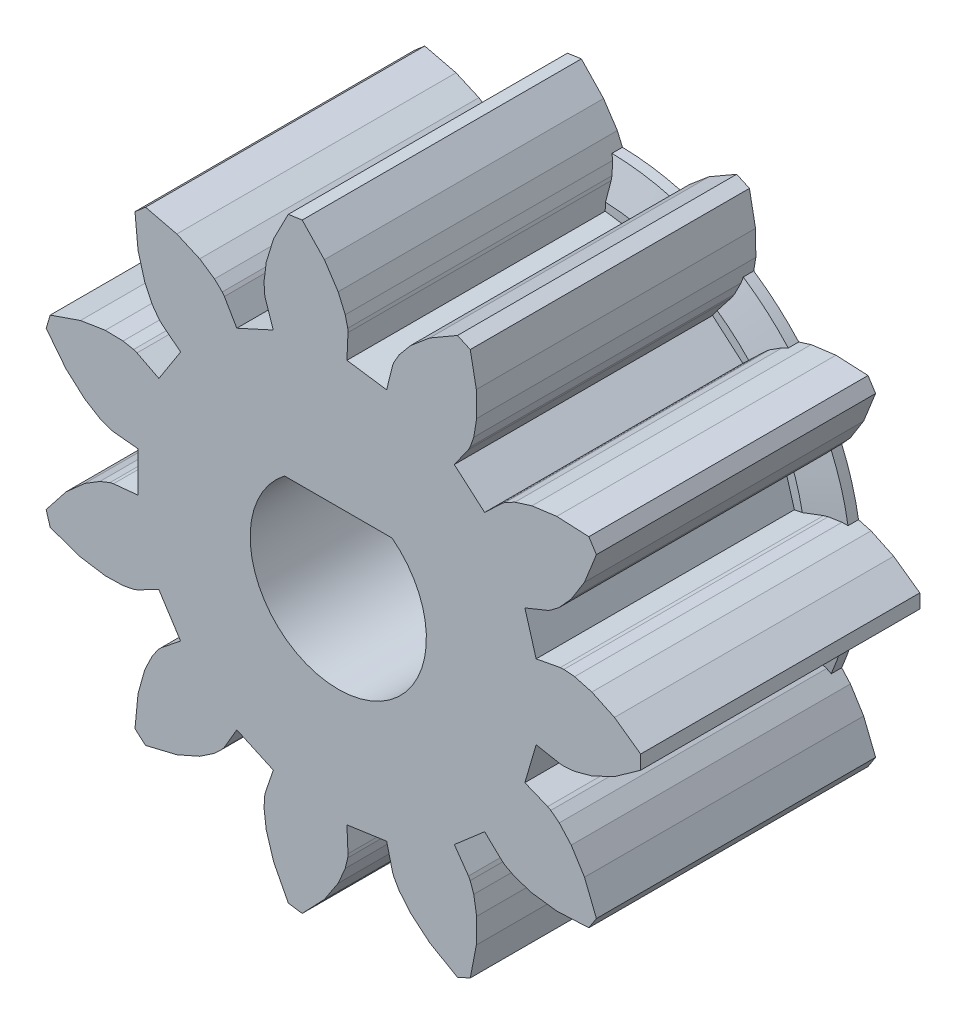
SolidWorks part; units mm, degrees
material "Custom Plastic"
ref_plane "Front Plane" through (0, 0, 0) normal (0, 0, 1) x (1, 0, 0)
ref_plane "Top Plane" through (0, 0, 0) normal (0, 1, 0) x (1, 0, 0)
ref_plane "Right Plane" through (0, 0, 0) normal (1, 0, 0) x (0, 0, -1)
sketch "Model" plane through (0, 0, 0) normal (0, 0, 1) x (1, 0, 0)
  line L0 (-8.37, -2.248) -> (-7.801, -1.524)
  line L1 (-7.801, -1.524) -> (-7.265, -1.048)
  line L2 (-7.265, -1.048) -> (-6.829, -0.78)
  line L3 (-6.829, -0.78) -> (-6.543, -0.667)
  line L4 (-6.543, -0.667) -> (-6.442, -0.645)
  line L5 (-6.442, -0.645) -> (-5.741, -0.575)
  line L6 (-5.741, -0.575) -> (-5.741, 0.575)
  line L7 (-5.741, 0.575) -> (-6.442, 0.645)
  line L8 (-6.442, 0.645) -> (-6.543, 0.667)
  line L9 (-6.543, 0.667) -> (-6.829, 0.78)
  line L10 (-6.829, 0.78) -> (-7.265, 1.048)
  line L11 (-7.265, 1.048) -> (-7.801, 1.524)
  line L12 (-7.801, 1.524) -> (-8.37, 2.248)
  line L13 (-8.37, 2.248) -> (-8.256, 2.634)
  line L14 (-8.256, 2.634) -> (-7.386, 2.935)
  line L15 (-7.386, 2.935) -> (-6.678, 3.046)
  line L16 (-6.678, 3.046) -> (-6.167, 3.035)
  line L17 (-6.167, 3.035) -> (-5.865, 2.976)
  line L18 (-5.865, 2.976) -> (-5.768, 2.94)
  line L19 (-5.768, 2.94) -> (-5.14, 2.62)
  line L20 (-5.14, 2.62) -> (-4.518, 3.587)
  line L21 (-4.518, 3.587) -> (-5.071, 4.026)
  line L22 (-5.071, 4.026) -> (-5.143, 4.099)
  line L23 (-5.143, 4.099) -> (-5.323, 4.348)
  line L24 (-5.323, 4.348) -> (-5.545, 4.81)
  line L25 (-5.545, 4.81) -> (-5.738, 5.5)
  line L26 (-5.738, 5.5) -> (-5.826, 6.416)
  line L27 (-5.826, 6.416) -> (-5.522, 6.679)
  line L28 (-5.522, 6.679) -> (-4.627, 6.462)
  line L29 (-4.627, 6.462) -> (-3.971, 6.173)
  line L30 (-3.971, 6.173) -> (-3.547, 5.887)
  line L31 (-3.547, 5.887) -> (-3.325, 5.674)
  line L32 (-3.325, 5.674) -> (-3.263, 5.592)
  line L33 (-3.263, 5.592) -> (-2.908, 4.983)
  line L34 (-2.908, 4.983) -> (-1.862, 5.461)
  line L35 (-1.862, 5.461) -> (-2.089, 6.128)
  line L36 (-2.089, 6.128) -> (-2.111, 6.229)
  line L37 (-2.111, 6.229) -> (-2.127, 6.536)
  line L38 (-2.127, 6.536) -> (-2.064, 7.044)
  line L39 (-2.064, 7.044) -> (-1.854, 7.729)
  line L40 (-1.854, 7.729) -> (-1.432, 8.547)
  line L41 (-1.432, 8.547) -> (-1.034, 8.604)
  line L42 (-1.034, 8.604) -> (-0.399, 7.938)
  line L43 (-0.399, 7.938) -> (-0.004, 7.34)
  line L44 (-0.004, 7.34) -> (0.199, 6.87)
  line L45 (0.199, 6.87) -> (0.271, 6.571)
  line L46 (0.271, 6.571) -> (0.278, 6.468)
  line L47 (0.278, 6.468) -> (0.248, 5.764)
  line L48 (0.248, 5.764) -> (1.386, 5.601)
  line L49 (1.386, 5.601) -> (1.555, 6.285)
  line L50 (1.555, 6.285) -> (1.592, 6.381)
  line L51 (1.592, 6.381) -> (1.744, 6.648)
  line L52 (1.744, 6.648) -> (2.071, 7.042)
  line L53 (2.071, 7.042) -> (2.619, 7.504)
  line L54 (2.619, 7.504) -> (3.416, 7.965)
  line L55 (3.416, 7.965) -> (3.782, 7.798)
  line L56 (3.782, 7.798) -> (3.956, 6.893)
  line L57 (3.956, 6.893) -> (3.965, 6.177)
  line L58 (3.965, 6.177) -> (3.882, 5.672)
  line L59 (3.882, 5.672) -> (3.78, 5.382)
  line L60 (3.78, 5.382) -> (3.731, 5.291)
  line L61 (3.731, 5.291) -> (3.325, 4.715)
  line L62 (3.325, 4.715) -> (4.194, 3.962)
  line L63 (4.194, 3.962) -> (4.706, 4.446)
  line L64 (4.706, 4.446) -> (4.789, 4.508)
  line L65 (4.789, 4.508) -> (5.062, 4.65)
  line L66 (5.062, 4.65) -> (5.55, 4.804)
  line L67 (5.55, 4.804) -> (6.26, 4.897)
  line L68 (6.26, 4.897) -> (7.18, 4.853)
  line L69 (7.18, 4.853) -> (7.397, 4.515)
  line L70 (7.397, 4.515) -> (7.055, 3.66)
  line L71 (7.055, 3.66) -> (6.675, 3.053)
  line L72 (6.675, 3.053) -> (6.332, 2.673)
  line L73 (6.332, 2.673) -> (6.09, 2.484)
  line L74 (6.09, 2.484) -> (6, 2.434)
  line L75 (6, 2.434) -> (5.347, 2.169)
  line L76 (5.347, 2.169) -> (5.67, 1.066)
  line L77 (5.67, 1.066) -> (6.363, 1.196)
  line L78 (6.363, 1.196) -> (6.466, 1.203)
  line L79 (6.466, 1.203) -> (6.772, 1.175)
  line L80 (6.772, 1.175) -> (7.266, 1.041)
  line L81 (7.266, 1.041) -> (7.914, 0.735)
  line L82 (7.914, 0.735) -> (8.664, 0.201)
  line L83 (8.664, 0.201) -> (8.664, -0.201)
  line L84 (8.664, -0.201) -> (7.914, -0.735)
  line L85 (7.914, -0.735) -> (7.266, -1.041)
  line L86 (7.266, -1.041) -> (6.772, -1.175)
  line L87 (6.772, -1.175) -> (6.466, -1.203)
  line L88 (6.466, -1.203) -> (6.363, -1.196)
  line L89 (6.363, -1.196) -> (5.67, -1.066)
  line L90 (5.67, -1.066) -> (5.346, -2.169)
  line L91 (5.346, -2.169) -> (6, -2.434)
  line L92 (6, -2.434) -> (6.09, -2.484)
  line L93 (6.09, -2.484) -> (6.332, -2.673)
  line L94 (6.332, -2.673) -> (6.675, -3.053)
  line L95 (6.675, -3.053) -> (7.055, -3.66)
  line L96 (7.055, -3.66) -> (7.397, -4.515)
  line L97 (7.397, -4.515) -> (7.18, -4.853)
  line L98 (7.18, -4.853) -> (6.26, -4.897)
  line L99 (6.26, -4.897) -> (5.55, -4.804)
  line L100 (5.55, -4.804) -> (5.062, -4.65)
  line L101 (5.062, -4.65) -> (4.789, -4.508)
  line L102 (4.789, -4.508) -> (4.706, -4.446)
  line L103 (4.706, -4.446) -> (4.194, -3.962)
  line L104 (4.194, -3.962) -> (3.325, -4.715)
  line L105 (3.325, -4.715) -> (3.731, -5.291)
  line L106 (3.731, -5.291) -> (3.78, -5.382)
  line L107 (3.78, -5.382) -> (3.882, -5.672)
  line L108 (3.882, -5.672) -> (3.965, -6.177)
  line L109 (3.965, -6.177) -> (3.956, -6.893)
  line L110 (3.956, -6.893) -> (3.782, -7.798)
  line L111 (3.782, -7.798) -> (3.416, -7.965)
  line L112 (3.416, -7.965) -> (2.619, -7.504)
  line L113 (2.619, -7.504) -> (2.071, -7.042)
  line L114 (2.071, -7.042) -> (1.744, -6.648)
  line L115 (1.744, -6.648) -> (1.592, -6.381)
  line L116 (1.592, -6.381) -> (1.555, -6.285)
  line L117 (1.555, -6.285) -> (1.386, -5.601)
  line L118 (1.386, -5.601) -> (0.248, -5.764)
  line L119 (0.248, -5.764) -> (0.278, -6.468)
  line L120 (0.278, -6.468) -> (0.271, -6.571)
  line L121 (0.271, -6.571) -> (0.199, -6.87)
  line L122 (0.199, -6.87) -> (-0.004, -7.34)
  line L123 (-0.004, -7.34) -> (-0.399, -7.938)
  line L124 (-0.399, -7.938) -> (-1.034, -8.604)
  line L125 (-1.034, -8.604) -> (-1.432, -8.547)
  line L126 (-1.432, -8.547) -> (-1.854, -7.729)
  line L127 (-1.854, -7.729) -> (-2.064, -7.044)
  line L128 (-2.064, -7.044) -> (-2.127, -6.536)
  line L129 (-2.127, -6.536) -> (-2.111, -6.229)
  line L130 (-2.111, -6.229) -> (-2.089, -6.128)
  line L131 (-2.089, -6.128) -> (-1.862, -5.461)
  line L132 (-1.862, -5.461) -> (-2.908, -4.983)
  line L133 (-2.908, -4.983) -> (-3.263, -5.592)
  line L134 (-3.263, -5.592) -> (-3.325, -5.674)
  line L135 (-3.325, -5.674) -> (-3.547, -5.887)
  line L136 (-3.547, -5.887) -> (-3.971, -6.173)
  line L137 (-3.971, -6.173) -> (-4.627, -6.462)
  line L138 (-4.627, -6.462) -> (-5.522, -6.679)
  line L139 (-5.522, -6.679) -> (-5.826, -6.416)
  line L140 (-5.826, -6.416) -> (-5.738, -5.5)
  line L141 (-5.738, -5.5) -> (-5.545, -4.81)
  line L142 (-5.545, -4.81) -> (-5.323, -4.348)
  line L143 (-5.323, -4.348) -> (-5.143, -4.099)
  line L144 (-5.143, -4.099) -> (-5.071, -4.026)
  line L145 (-5.071, -4.026) -> (-4.519, -3.587)
  line L146 (-4.519, -3.587) -> (-5.141, -2.62)
  line L147 (-5.141, -2.62) -> (-5.768, -2.94)
  line L148 (-5.768, -2.94) -> (-5.865, -2.976)
  line L149 (-5.865, -2.976) -> (-6.167, -3.035)
  line L150 (-6.167, -3.035) -> (-6.678, -3.046)
  line L151 (-6.678, -3.046) -> (-7.386, -2.935)
  line L152 (-7.386, -2.935) -> (-8.256, -2.634)
  line L153 (-8.256, -2.634) -> (-8.37, -2.248)
extrude "Boss-Extrude1" add sketch "Model" along normal blind 8
sketch "Sketch2" plane through (0, 0, 8) normal (0, 0, 1) x (1, 0, 0)
  line L0 (0, 0) -> (0, 2) construction
  line L1 (-1.5413, 2) -> (1.5413, 2)
  arc A0 (-1.5413, 2) -> (1.5413, 2) centre (0, 0) ccw
  dimension "D1" = 5.05
  dimension "D2" = 2
extrude "Cut-Extrude1" cut sketch "Sketch2" against normal through all
sketch "Sketch3" plane through (0, 0, 0) normal (0, 1, 0) x (1, 0, 0)
  line L0 (3.2, 0) -> (3.2, -0.6)
  line L1 (3.416, 0) -> (2.619, 0) construction
  line L2 (3.2, -0.6) -> (6, -0.6)
  line L5 (7, 0) -> (3.2, 0)
  line L6 (0, 0) -> (0, -5.7452) construction
  line L7 (7, 0) -> (7, -0.3)
  line L8 (7, -0.3) -> (6, -0.6)
  dimension "D1" = 3.2
  dimension "D2" = 0.3
  dimension "D3" = 0.6
  dimension "D4" = 7
  dimension "D5" = 1
revolve "Revolve1" add sketch "Sketch3" angle 360 about L6
chamfer "Chamfer1" distance 1 angle 30 2 edges at (0, 2, 0) (0, -2.525, 0)
